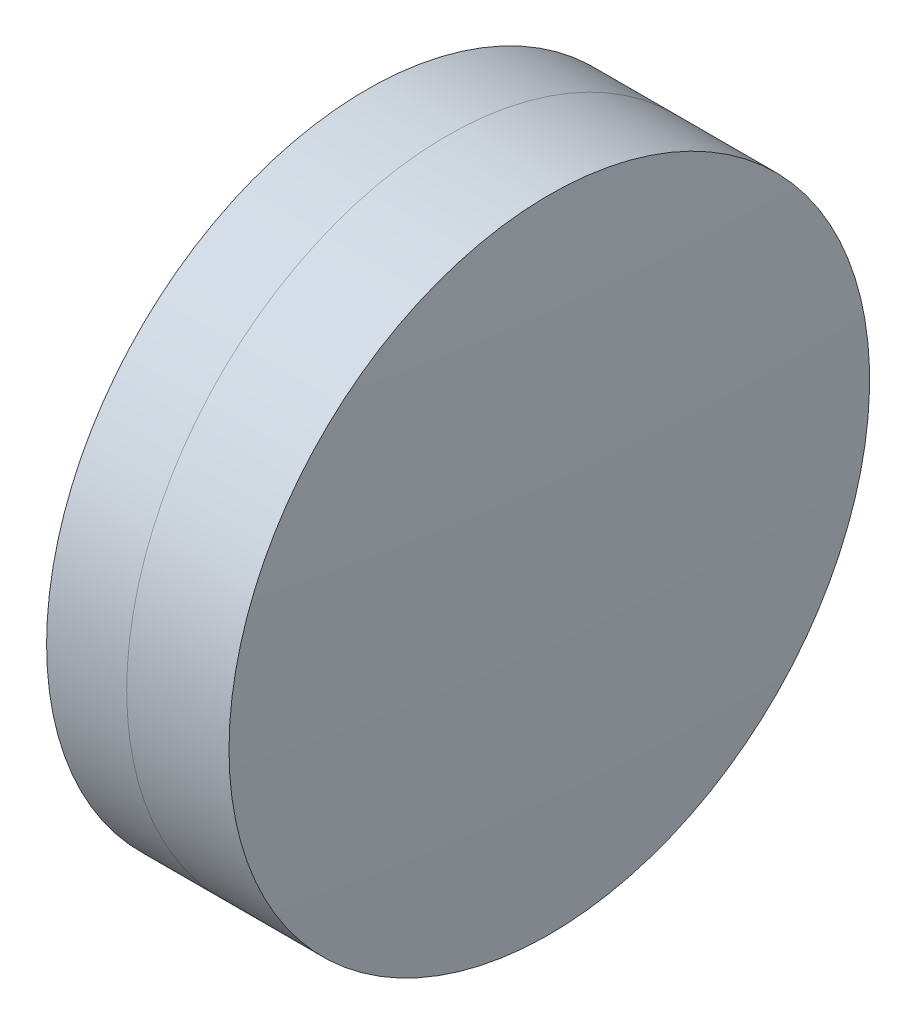
SolidWorks part; units mm, degrees
ref_plane "前视基准面" through (0, 0, 0) normal (0, 0, 1) x (1, 0, 0)
ref_plane "上视基准面" through (0, 0, 0) normal (0, 1, 0) x (1, 0, 0)
ref_plane "右视基准面" through (0, 0, 0) normal (1, 0, 0) x (0, 0, -1)
sketch "草图1" plane through (0, 0, 0) normal (0, 1, 0) x (1, 0, 0)
  line L0 (-9.7026, 0) -> (42.9866, 0) construction
  line L1 (33.615, -8) -> (35.6165, -8)
  line L2 (33.615, 8) -> (35.6165, 8)
  arc A0 (35.6165, -8) -> (35.6165, 8) centre (-3.9947, 0) ccw
  arc A1 (33.615, 8) -> (33.615, -8) centre (95.0503, 0) ccw
  point P10 (33.0963, 0)
  point P11 (36.4163, 0)
  dimension "D3" = 61.954
  dimension "D4" = 40.411
  dimension "D1" = 8
  dimension "D2" = 8
  dimension "D5" = 3.32
revolve "旋转1" add sketch "草图1" angle 360 about L0
sketch "草图2" plane through (0, 0, 0) normal (0, 1, 0) x (1, 0, 0)
  line L0 (-0.5519, 0) -> (39.8216, 0) construction
  line L2 (35.6165, 8) -> (38.1709, 8)
  line L3 (35.6165, -8) -> (38.1709, -8)
  arc A0 (38.1709, -8) -> (38.1709, 8) centre (-92.1247, 0) ccw
  arc A1 (35.6165, -8) -> (35.6165, 8) centre (-3.9947, 0) ccw construction
  arc A2 (35.6165, -8) -> (35.6165, 8) centre (-3.9947, 0) ccw
  point P4 (36.4163, 0)
  point P8 (38.4163, 0)
  point P9 (39.8216, 0)
  dimension "D1" = 130.541
  dimension "D2" = 2
revolve "旋转3" add sketch "草图2" angle 360 about L0
